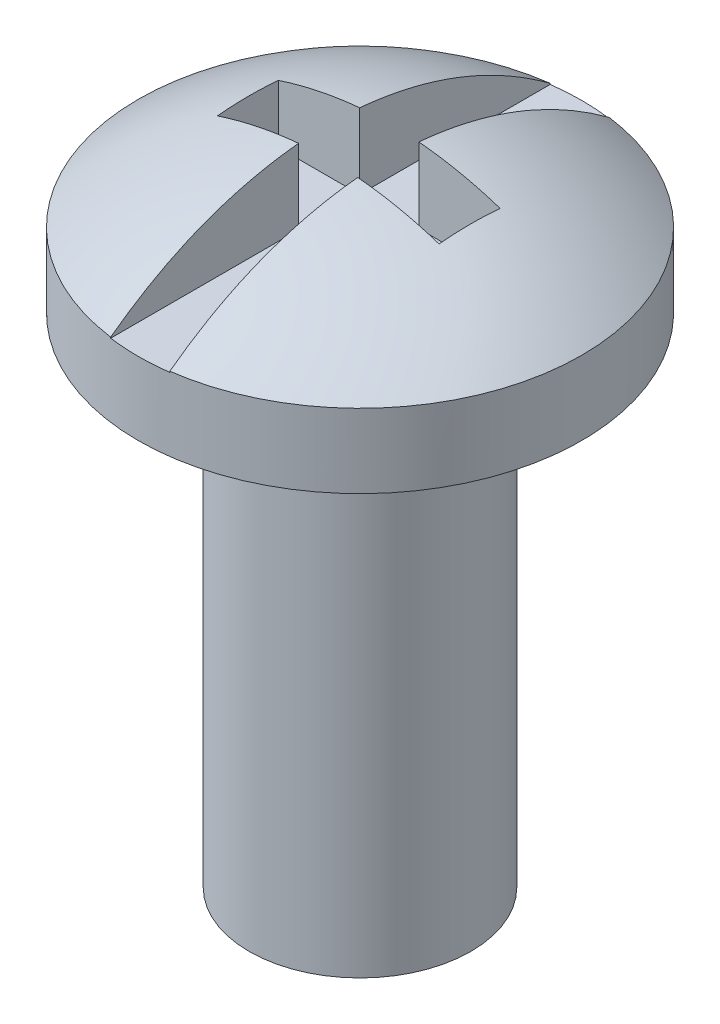
SolidWorks part; units mm, degrees
material "Zinklegierung 7; AG40B; Zn-4Al-0.015Mg"
ref_plane "Ebene vorne" through (0, 0, 0) normal (0, 0, 1) x (1, 0, 0)
ref_plane "Ebene oben" through (0, 0, 0) normal (0, 1, 0) x (1, 0, 0)
ref_plane "Ebene rechts" through (0, 0, 0) normal (1, 0, 0) x (0, 0, -1)
sketch "Skizze1" plane through (0, 0, 0) normal (0, 0, 1) x (1, 0, 0)
  line L0 (0, 54.4769) -> (0, -52.0058) construction
  line L1 (-3, -0.9869) -> (-1.5, -0.9869)
  line L2 (-3, 0.0131) -> (-3, -0.9869)
  line L3 (-1.5, -0.9869) -> (-1.5, -7.7222)
  line L4 (-1.5, -7.7222) -> (0, -7.7222)
  line L5 (0, 1.0562) -> (0, -7.7222)
  spline S0 degree 2 poles (-3, 0.0131) (-1.655, 1.0201) (0, 1.0562) knots 0 0 0 0.690588 0.690588 0.690588
  dimension "D1" = 3
  dimension "D2" = 1
  dimension "D3" = 3
revolve "Rotation1" add sketch "Skizze1" angle 360 about L0
sketch "Skizze2" plane through (0, 0, 0) normal (0, 1, 0) x (1, 0, 0)
  line L0 (0, 4.5397) -> (0, 3.5737) construction
  line L1 (-4.2311, 0) -> (-1.5, 0) construction
  line L2 (-0.4, 3.5737) -> (0.4, 3.5737)
  line L3 (-0.4, 3.5737) -> (-0.4, 0.3956)
  line L4 (-0.4, -3.4125) -> (0.4, -3.4125)
  line L5 (0.4, 3.5737) -> (0.4, 0.3956)
  line L6 (0.4, 0.3956) -> (1.5, 0.3956)
  line L7 (-1.5, 0.3956) -> (-0.4, 0.3956)
  line L8 (-1.5, 0.3956) -> (-1.5, -0.4304)
  line L9 (-1.5, -0.4304) -> (-0.4, -0.4304)
  line L10 (1.5, 0.3956) -> (1.5, -0.4304)
  line L11 (-0.4, -0.4304) -> (-0.4, -3.4125)
  line L12 (-0.4, 0) -> (0.4, 0) construction
  line L13 (0.4, -0.4304) -> (1.5, -0.4304)
  line L14 (0.4, -0.4304) -> (0.4, -3.4125)
  line L15 (1.5, 0) -> (4.6031, 0) construction
  line L16 (0, 0) -> (0, -0.4304) construction
  dimension "D1" = 0.8
  dimension "D2" = 3
extrude "Schnitt-Linear austragen1" cut sketch "Skizze2" along normal through all
